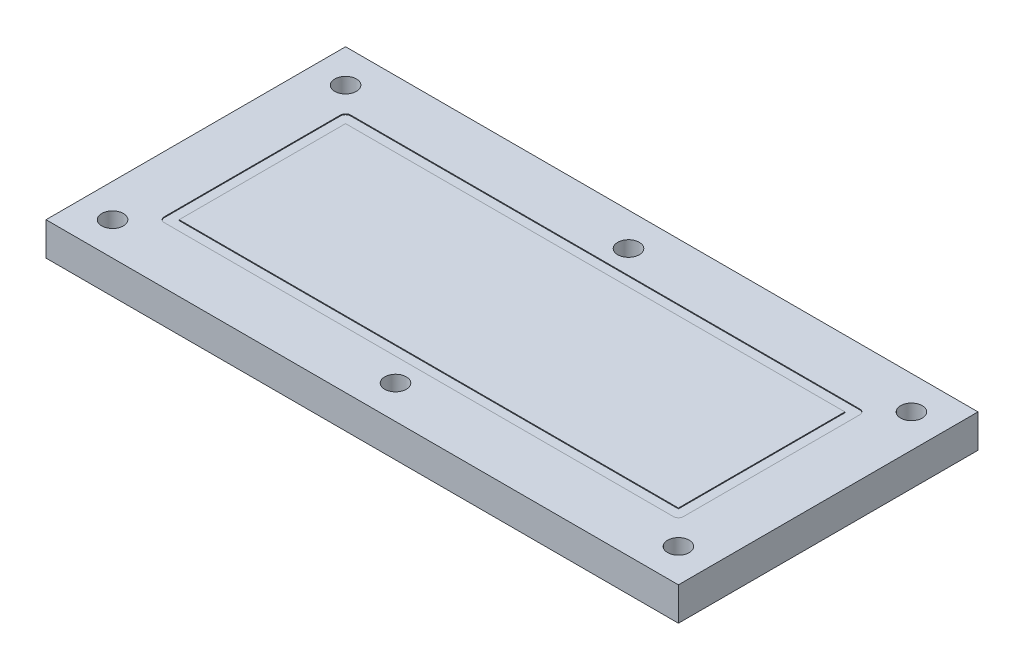
SolidWorks part; units mm, degrees
material "Plain Carbon Steel"
ref_plane "Front Plane" through (0, 0, 0) normal (0, 0, 1) x (1, 0, 0)
ref_plane "Top Plane" through (0, 0, 0) normal (0, 1, 0) x (1, 0, 0)
ref_plane "Right Plane" through (0, 0, 0) normal (1, 0, 0) x (0, 0, -1)
sketch "Sketch1" plane through (0, 0, 0) normal (0, 1, 0) x (1, 0, 0)
  line L1 (-190, -90) -> (190, -90)
  line L2 (-190, -90) -> (-190, 90)
  line L3 (-190, 90) -> (190, 90)
  line L4 (190, -90) -> (190, 90)
  line L5 (-190, -90) -> (190, 90) construction
  line L6 (-190, 90) -> (190, -90) construction
  point P0 (0, 0)
  dimension "D1" = 180
  dimension "D2" = 380
extrude "Boss-Extrude1" add sketch "Sketch1" along normal blind 20
sketch "Sketch2" plane through (0, 20, 0) normal (0, 1, 0) x (1, 0, 0)
  line L0 (0, -11) -> (0, 11) construction
  circle A0 centre (-170, 70) radius 6.5
  circle A1 centre (-170, -70) radius 6.5
  circle A2 centre (0, -70) radius 6.5
  circle A3 centre (0, 70) radius 6.5
  circle A4 centre (170, -70) radius 6.5
  circle A5 centre (170, 70) radius 6.5
  dimension "D1" = 13
  dimension "D2" = 13
  dimension "D3" = 13
  dimension "D4" = 13
extrude "Cut-Extrude1" cut sketch "Sketch2" against normal through all
sketch "Sketch3" plane through (0, 20, 0) normal (0, 1, 0) x (1, 0, 0)
  line L1 (-153, -56) -> (153, -56)
  line L2 (-156, -53) -> (-156, 53)
  line L3 (-153, 56) -> (153, 56)
  line L4 (156, -53) -> (156, 53)
  line L5 (-156, -56) -> (156, 56) construction
  line L6 (-156, 56) -> (156, -56) construction
  line L7 (-150, -50) -> (150, -50)
  line L8 (-150, -50) -> (-150, 50)
  line L9 (-150, 50) -> (150, 50)
  line L10 (150, -50) -> (150, 50)
  line L11 (-150, -50) -> (150, 50) construction
  line L12 (-150, 50) -> (150, -50) construction
  arc A0 (153, 56) -> (156, 53) centre (153, 53) cw
  arc A1 (153, -56) -> (156, -53) centre (153, -53) ccw
  arc A2 (-153, -56) -> (-156, -53) centre (-153, -53) cw
  arc A3 (-156, 53) -> (-153, 56) centre (-153, 53) cw
  point P0 (0, 0)
  point P6 (0, 0)
  dimension "D5" = 3
  dimension "D1" = 300
  dimension "D2" = 100
  dimension "D3" = 6
  dimension "D4" = 6
extrude "Cut-Extrude2" cut sketch "Sketch3" against normal blind 0.5
